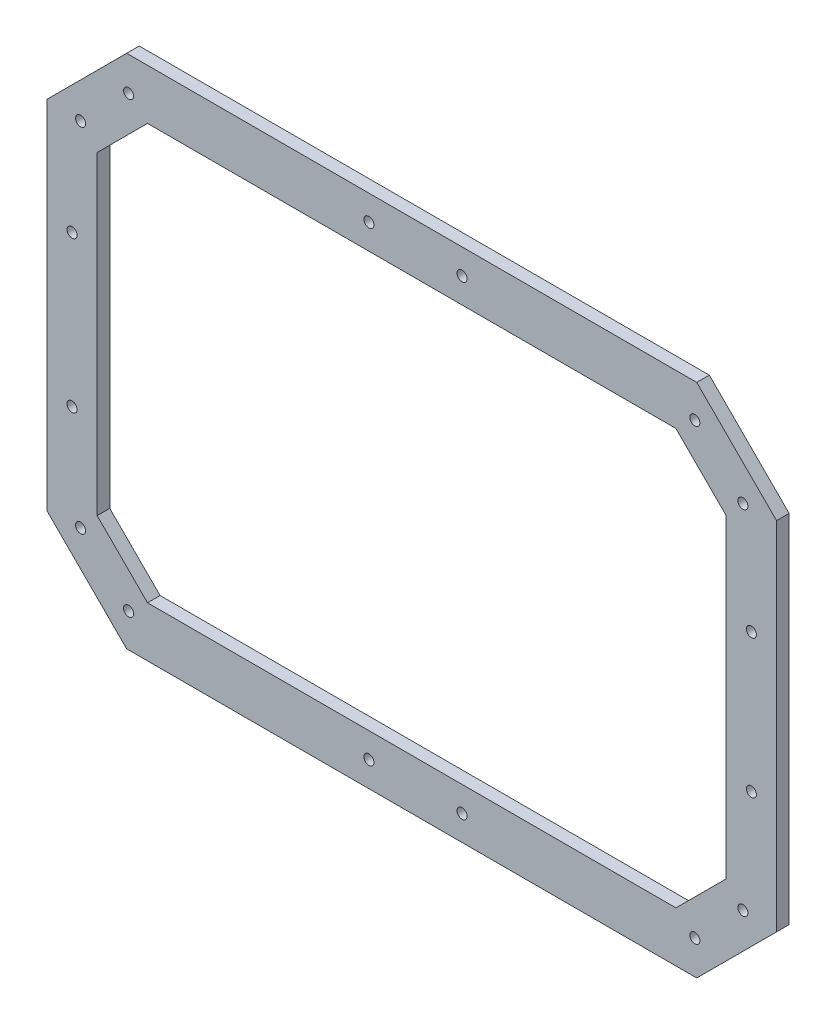
SolidWorks part; units mm, degrees
ref_plane "Front Plane" through (0, 0, 0) normal (0, 0, 1) x (1, 0, 0)
ref_plane "Top Plane" through (0, 0, 0) normal (0, 1, 0) x (1, 0, 0)
ref_plane "Right Plane" through (0, 0, 0) normal (1, 0, 0) x (0, 0, -1)
sketch "Sketch1" plane through (0, 0, 0) normal (0, 0, 1) x (1, 0, 0)
  line L0 (-89.0123, 85.6163) -> (120.9877, 85.6163)
  line L1 (140.9877, 65.6163) -> (140.9877, -59.3837)
  line L2 (120.9877, -79.3837) -> (-89.0123, -79.3837)
  line L3 (-109.0123, 65.6163) -> (-109.0123, -59.3837)
  line L4 (-109.0123, 65.6163) -> (-89.0123, 85.6163)
  line L5 (120.9877, 85.6163) -> (140.9877, 65.6163)
  line L6 (-89.0123, -79.3837) -> (-109.0123, -59.3837)
  line L7 (140.9877, -59.3837) -> (120.9877, -79.3837)
  line L8 (-97.2965, 105.6163) -> (129.272, 105.6163)
  line L9 (129.272, 105.6163) -> (160.9877, 73.9005)
  line L10 (160.9877, 73.9005) -> (160.9877, -67.668)
  line L11 (160.9877, -67.668) -> (129.272, -99.3837)
  line L12 (129.272, -99.3837) -> (-97.2965, -99.3837)
  line L13 (-97.2965, -99.3837) -> (-129.0123, -67.668)
  line L14 (-129.0123, 73.9005) -> (-129.0123, -67.668)
  line L15 (-129.0123, 73.9005) -> (-97.2965, 105.6163)
  line L16 (-89.0123, 85.6163) -> (-89.0123, -79.3837)
  line L17 (120.9877, 85.6163) -> (120.9877, -79.3837)
  line L18 (-109.0123, 65.6163) -> (-113.1544, 61.4741)
  line L19 (-89.0123, 85.6163) -> (-84.8701, 89.7584)
  line L20 (-99.0123, 103.9005) -> (-84.8701, 89.7584)
  line L21 (-127.2965, 75.6163) -> (-113.1544, 61.4741)
  line L22 (-113.1544, 89.7584) -> (-99.0123, 75.6163)
  line L23 (-113.1544, -55.2416) -> (-109.0123, -59.3837)
  line L24 (-89.0123, -79.3837) -> (-84.8701, -83.5259)
  line L25 (-84.8701, -83.5259) -> (-99.0123, -97.668)
  line L26 (-113.1544, -55.2416) -> (-127.2965, -69.3837)
  line L27 (-99.0123, -69.3837) -> (-113.1544, -83.5259)
  line L28 (120.9877, -79.3837) -> (116.8456, -83.5259)
  line L29 (140.9877, -59.3837) -> (145.1299, -55.2416)
  line L30 (145.1299, -55.2416) -> (159.272, -69.3837)
  line L31 (116.8456, -83.5259) -> (130.9877, -97.668)
  line L32 (130.9877, -69.3837) -> (145.1299, -83.5259)
  line L33 (120.9877, 85.6163) -> (116.8456, 89.7584)
  line L34 (140.9877, 65.6163) -> (145.1299, 61.4741)
  line L35 (145.1299, 61.4741) -> (159.272, 75.6163)
  line L36 (130.9877, 103.9005) -> (116.8456, 89.7584)
  line L37 (145.1299, 89.7584) -> (130.9877, 75.6163)
  line L38 (-11.0123, 105.6163) -> (-11.0123, 85.6163)
  line L39 (45.9877, 105.6163) -> (45.9877, 85.6163)
  line L40 (-11.0123, -79.3837) -> (-11.0123, -99.3837)
  line L41 (45.9877, -79.3837) -> (45.9877, -99.3837)
  line L42 (15.9877, -79.3837) -> (15.9877, -99.3837)
  line L43 (140.9877, 38.1163) -> (160.9877, 38.1163)
  line L44 (140.9877, -31.8837) -> (160.9877, -31.8837)
  line L45 (-130.4156, 43.1163) -> (-109.0123, 43.1163)
  line L46 (-109.0123, -36.8837) -> (-129.0123, -36.8837)
  circle A0 centre (128.5129, 92.2333) radius 2
  circle A1 centre (147.6047, 73.1414) radius 2
  circle A2 centre (-96.5374, 92.2333) radius 2
  circle A3 centre (-96.5374, -86.0008) radius 2
  circle A4 centre (-115.6293, 73.1414) radius 2
  circle A5 centre (-115.6293, -66.9089) radius 2
  circle A6 centre (128.5129, -86.0008) radius 2
  circle A7 centre (147.6047, -66.9089) radius 2
  circle A8 centre (35.9877, 95.6163) radius 2
  circle A9 centre (35.9877, -89.3837) radius 2
  circle A10 centre (-1.0123, -89.3837) radius 2
  circle A11 centre (-1.0123, 95.6163) radius 2
  circle A12 centre (150.9877, 30.6163) radius 2
  circle A13 centre (150.9877, -24.3837) radius 2
  circle A14 centre (-119.0123, 33.1163) radius 2
  circle A15 centre (-119.0123, -26.8837) radius 2
  point P0 (-109.0123, 85.6163)
  point P1 (140.9877, 85.6163)
  point P2 (140.9877, -79.3837)
  point P4 (-109.0123, -79.3837)
  point P20 (-99.0123, 75.6163)
  point P21 (-113.1544, 61.4741)
  point P22 (-84.8701, 89.7584)
  point P23 (-113.1544, 89.7584)
  point P24 (-99.0123, 103.9005)
  point P25 (-127.2965, 75.6163)
  point P32 (-99.0123, -69.3837)
  point P33 (-113.1544, -83.5259)
  point P34 (-113.1544, -55.2416)
  point P35 (-84.8701, -83.5259)
  point P36 (-99.0123, -97.668)
  point P37 (-127.2965, -69.3837)
  point P44 (130.9877, -69.3837)
  point P45 (145.1299, -83.5259)
  point P46 (116.8456, -83.5259)
  point P47 (145.1299, -55.2416)
  point P48 (159.272, -69.3837)
  point P49 (130.9877, -97.668)
  point P50 (130.9877, -69.3837)
  point P51 (116.8456, -83.5259)
  point P58 (130.9877, 75.6163)
  point P59 (145.1299, 89.7584)
  point P60 (130.9877, 103.9005)
  point P61 (159.272, 75.6163)
  point P62 (145.1299, 61.4741)
  point P63 (116.8456, 89.7584)
  point P86 (15.9877, 105.6163)
  point P87 (45.9877, 105.6163)
  point P88 (-11.0123, 105.6163)
  point P89 (-11.0123, 85.6163)
  point P90 (45.9877, 85.6163)
  point P95 (15.9877, -79.3837)
  point P96 (15.9877, -99.3837)
  point P97 (45.9877, -99.3837)
  point P98 (15.9877, 85.6163)
  point P99 (-11.0123, -99.3837)
  point P100 (-11.0123, -79.3837)
  point P101 (45.9877, -79.3837)
  point P116 (140.9877, 3.1163)
  point P117 (160.9877, 3.1163)
  point P118 (160.9877, 38.1163)
  point P119 (140.9877, 38.1163)
  point P120 (140.9877, -31.8837)
  point P121 (160.9877, -31.8837)
  point P128 (-89.0123, 3.1163)
  point P135 (-129.0123, 3.1163)
  point P136 (-109.0123, 43.1163)
  point P137 (-109.0123, 3.1163)
  point P138 (-109.0123, -36.8837)
  point P139 (-129.0123, -36.8837)
  point P140 (-129.0123, 43.1163)
  dimension "D26" = 4
  dimension "D51" = 4
  dimension "D64" = 4
  dimension "D77" = 4
  dimension "D78" = 4
  dimension "D79" = 4
  dimension "D80" = 4
  dimension "D81" = 4
  dimension "D82" = 4
  dimension "D83" = 4
  dimension "D84" = 4
  dimension "D85" = 4
  dimension "D86" = 4
  dimension "D87" = 4
  dimension "D88" = 4
  dimension "D89" = 4
  dimension "D90" = 4
  dimension "D91" = 4
  dimension "D92" = 4
  dimension "D1" = 20
  dimension "D2" = 45
  dimension "D3" = 20
  dimension "D4" = 45
  dimension "D5" = 20
  dimension "D6" = 45
  dimension "D7" = 20
  dimension "D8" = 45
  dimension "D9" = 125
  dimension "D10" = 20
  dimension "D11" = 20
  dimension "D12" = 20
  dimension "D13" = 20
  dimension "D14" = 20
  dimension "D15" = 20
  dimension "D16" = 20
  dimension "D17" = 20
  dimension "D18" = 20
  dimension "D19" = 20
  dimension "D20" = 20
  dimension "D21" = 20
  dimension "D22" = 20
  dimension "D23" = 20
  dimension "D24" = 20
  dimension "D25" = 20
  dimension "D27" = 6.5
  dimension "D28" = 27
  dimension "D29" = 10
  dimension "D30" = 10
  dimension "D31" = 6.5
  dimension "D32" = 10
  dimension "D33" = 10
  dimension "D34" = 6.5
  dimension "D35" = 10
  dimension "D36" = 10
  dimension "D37" = 6.5
  dimension "D38" = 27
  dimension "D39" = 10
  dimension "D40" = 10
  dimension "D41" = 6.5
  dimension "D42" = 27
  dimension "D43" = 27
  dimension "D44" = 30
  dimension "D45" = 27
  dimension "D46" = 30
  dimension "D47" = 27
  dimension "D48" = 30
  dimension "D49" = 27
  dimension "D50" = 30
  dimension "D52" = 10
  dimension "D53" = 10
  dimension "D54" = 37
  dimension "D55" = 10
  dimension "D56" = 10
  dimension "D57" = 10
  dimension "D58" = 10
  dimension "D59" = 37
  dimension "D60" = 35
  dimension "D61" = 35
  dimension "D62" = 35
  dimension "D63" = 35
  dimension "D65" = 10
  dimension "D66" = 7.5
  dimension "D67" = 10
  dimension "D68" = 55
  dimension "D69" = 40
  dimension "D70" = 40
  dimension "D71" = 40
  dimension "D72" = 40
  dimension "D73" = 10
  dimension "D74" = 10
  dimension "D75" = 10
  dimension "D76" = 60
extrude "Boss-Extrude1" add sketch "Sketch1" along normal blind 5 contours L3 L46 L14 L13 L26 L23 | L46 L3 L45 L14 A15 A14 | L27 L6 L23 L26 L13 A5 | L6 L27 L13 L25 L24 A3 | L40 L2 L24 L25 L13 L12 | L42 L2 L40 L12 A10 | L2 L42 L12 L41 A9 | L2 L41 L12 L11 L31 L28 | L32 L7 L28 L31 L11 A6 | L7 L32 L11 L30 L29 A7 | L44 L1 L29 L30 L11 L10 | L1 L44 L10 L43 A13 A12 | L1 L43 L10 L9 L35 L34 | L9 L37 L5 L34 L35 A1 | L37 L9 L36 L33 L5 A0 | L8 L39 L0 L33 L36 L9 | L39 L8 L38 L0 A11 A8 | L38 L8 L15 L20 L19 L0 | L15 L22 L4 L19 L20 A2 | L22 L15 L21 L18 L4 A4 | L14 L45 L3 L18 L21 L15
